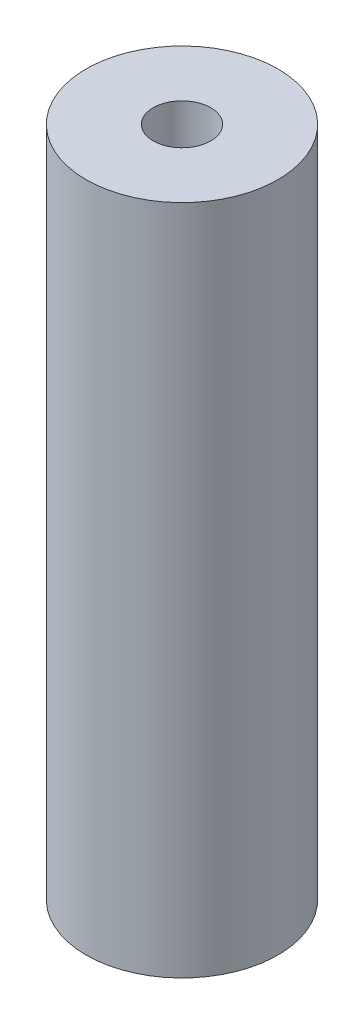
SolidWorks part; units mm, degrees
ref_plane "Front Plane" through (0, 0, 0) normal (0, 0, 1) x (1, 0, 0)
ref_plane "Top Plane" through (0, 0, 0) normal (0, 1, 0) x (1, 0, 0)
ref_plane "Right Plane" through (0, 0, 0) normal (1, 0, 0) x (0, 0, -1)
sketch "Sketch2" plane through (0, 0, 0) normal (0, 1, 0) x (1, 0, 0)
  circle A0 centre (0, 0) radius 5
  circle A1 centre (0, 0) radius 1.5
  dimension "D1" = 10
  dimension "D2" = 3
extrude "Boss-Extrude1" add sketch "Sketch2" along normal blind 35
